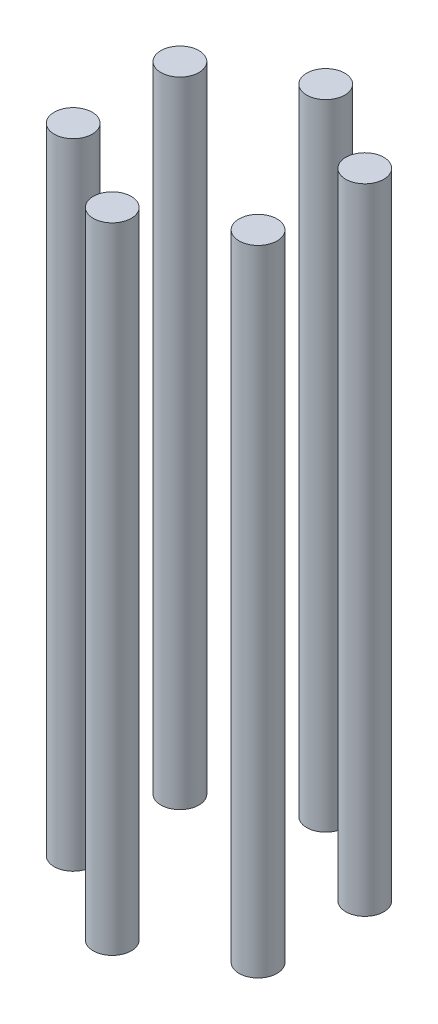
SolidWorks part; units mm, degrees
material "ASTM A36 Steel"
ref_plane "Front Plane" through (0, 0, 0) normal (0, 0, 1) x (1, 0, 0)
ref_plane "Top Plane" through (0, 0, 0) normal (0, 1, 0) x (1, 0, 0)
ref_plane "Right Plane" through (0, 0, 0) normal (1, 0, 0) x (0, 0, -1)
sketch "Sketch1" plane through (0, 0, 0) normal (0, 1, 0) x (1, 0, 0)
  circle A1 centre (0, -21.87) radius 3.9
  circle A2 centre (-18.9399, -10.935) radius 3.9
  circle A3 centre (-18.9399, 10.935) radius 3.9
  circle A4 centre (0, 21.87) radius 3.9
  circle A5 centre (18.9399, 10.935) radius 3.9
  circle A6 centre (18.9399, -10.935) radius 3.9
  point P14 (0, 0)
  dimension "D1" = 7.8
extrude "Boss-Extrude1" add sketch "Sketch1" along normal blind 130
